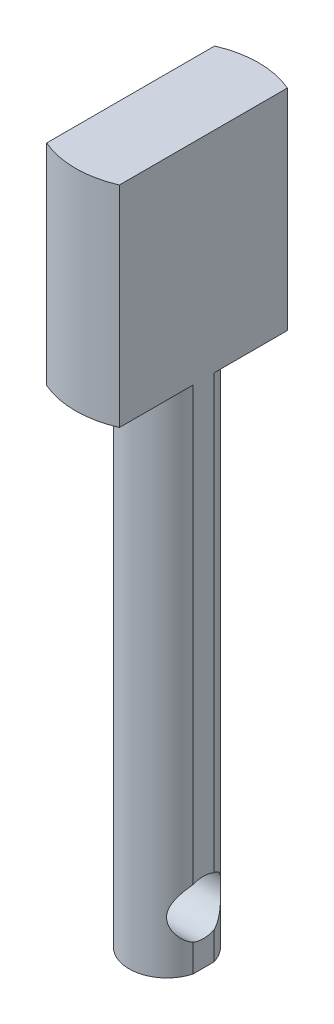
SolidWorks part; units mm, degrees
ref_plane "Front Plane" through (0, 0, 0) normal (0, 0, 1) x (1, 0, 0)
ref_plane "Top Plane" through (0, 0, 0) normal (0, 1, 0) x (1, 0, 0)
ref_plane "Right Plane" through (0, 0, 0) normal (1, 0, 0) x (0, 0, -1)
sketch "Sketch1" plane through (0, 0, 0) normal (0, 1, 0) x (1, 0, 0)
  circle A0 centre (0, 0) radius 2.525
  dimension "D1" = 5.05
extrude "Boss-Extrude1" add sketch "Sketch1" along normal blind 48
sketch "Sketch2" plane through (0, 48, 0) normal (0, 1, 0) x (1, 0, 0)
  circle A0 centre (0, 0) radius 6.1
  dimension "D1" = 12.2
extrude "Boss-Extrude2" add sketch "Sketch2" against normal blind 14
sketch "Sketch3" plane through (0, 0, 0) normal (1, 0, 0) x (0, 0, -1)
  line L0 (0, 0) -> (0, 3.5) construction
  line L1 (-2.525, 0) -> (2.525, 0) construction
  circle A0 centre (0, 3.5) radius 1.8
  dimension "D1" = 3.6
  dimension "D2" = 3.5
extrude "Cut-Extrude1" cut sketch "Sketch3" against normal through all both and the other way through all
sketch "Sketch4" plane through (0, 0, 0) normal (0, 1, 0) x (1, 0, 0)
  line L0 (0, 0) -> (-2.525, 0) construction
  line L1 (-2.425, 11.6888) -> (2.425, 11.6888)
  line L2 (-2.425, 11.6888) -> (-2.425, -11.6888)
  line L3 (-2.425, -11.6888) -> (2.425, -11.6888)
  line L4 (2.425, 11.6888) -> (2.425, -11.6888)
  line L5 (-2.425, 11.6888) -> (2.425, -11.6888) construction
  line L6 (-2.425, -11.6888) -> (2.425, 11.6888) construction
  line L7 (-2.525, 0) -> (-2.525, -2.1428) construction
  circle A0 centre (0, 0) radius 2.525 construction
  point P4 (0, 0)
  dimension "D1" = 0.1
extrude "Cut-Extrude4" cut sketch "Sketch4" along normal through all flip side to cut contours L4 L1 L2 L3
